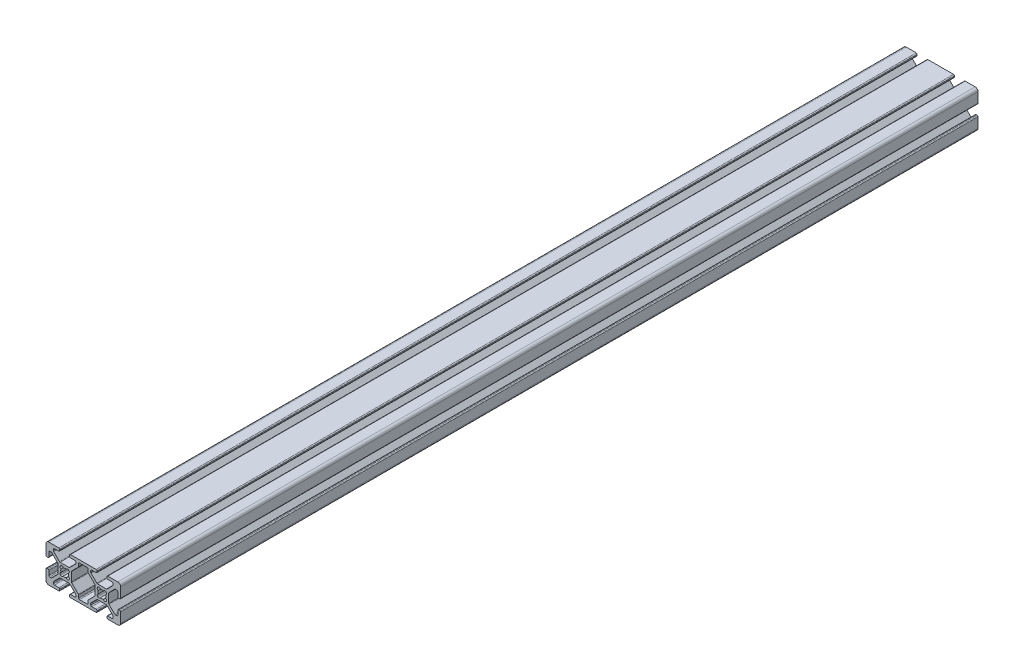
SolidWorks part; units mm, degrees
material "6105-T5 Aluminum"
ref_plane "Front Plane" through (0, 0, 0) normal (0, 0, 1) x (1, 0, 0)
ref_plane "Top Plane" through (0, 0, 0) normal (0, 1, 0) x (1, 0, 0)
ref_plane "Right Plane" through (0, 0, 0) normal (1, 0, 0) x (0, 0, -1)
sketch "Sketch1" plane through (0, 0, 0) normal (0, 0, 1) x (1, 0, 0)
  line L0 (-2.1249, -2.3045) -> (-2.3045, -2.1249)
  line L1 (-2.3045, 2.1249) -> (-2.1249, 2.3045)
  line L2 (2.1249, 2.3045) -> (2.3045, 2.1249)
  line L3 (2.3045, -2.1249) -> (2.1249, -2.3045)
  line L4 (-12.505, -7.992) -> (-12.505, -6.6448)
  line L5 (-12.6538, -6.2856) -> (-16.1962, -2.7431)
  line L6 (-16.345, -2.3839) -> (-16.345, 2.3839)
  line L7 (-16.1962, 2.7431) -> (-12.6538, 6.2856)
  line L8 (-12.505, 6.6448) -> (-12.505, 7.992)
  line L9 (-11.997, 8.5) -> (-8.003, 8.5)
  line L10 (-7.495, 7.992) -> (-7.495, 6.6448)
  line L11 (-7.3462, 6.2856) -> (-3.8038, 2.7431)
  line L12 (-3.655, 2.3839) -> (-3.655, -2.3839)
  line L13 (-3.8038, -2.7431) -> (-7.3462, -6.2856)
  line L14 (-7.495, -6.6448) -> (-7.495, -7.992)
  line L15 (-8.003, -8.5) -> (-11.997, -8.5)
  line L16 (-22.1249, -2.3045) -> (-22.3045, -2.1249)
  line L17 (-22.3045, 2.1249) -> (-22.1249, 2.3045)
  line L18 (-17.8751, 2.3045) -> (-17.6955, 2.1249)
  line L19 (-17.6955, -2.1249) -> (-17.8751, -2.3045)
  line L20 (-22.3839, -3.655) -> (-17.6161, -3.655)
  line L21 (-17.2569, -3.8038) -> (-14.1538, -6.9069)
  line L22 (-14.005, -7.2661) -> (-14.005, -7.992)
  line L23 (-14.513, -8.5) -> (-16.862, -8.5)
  line L24 (-17.37, -9.008) -> (-17.37, -9.492)
  line L25 (-16.862, -10) -> (-3.138, -10)
  line L26 (-2.63, -9.492) -> (-2.63, -9.008)
  line L27 (-3.138, -8.5) -> (-5.487, -8.5)
  line L28 (-5.995, -7.992) -> (-5.995, -7.2661)
  line L29 (-5.8462, -6.9069) -> (-2.7431, -3.8038)
  line L30 (-2.3839, -3.655) -> (2.3839, -3.655)
  line L31 (2.7431, -3.8038) -> (5.8462, -6.9069)
  line L32 (5.995, -7.2661) -> (5.995, -7.992)
  line L33 (5.487, -8.5) -> (3.138, -8.5)
  line L34 (2.63, -9.008) -> (2.63, -9.492)
  line L35 (3.138, -10) -> (8.5, -10)
  line L36 (10, -8.5) -> (10, -3.138)
  line L37 (9.492, -2.63) -> (9.008, -2.63)
  line L38 (8.5, -3.138) -> (8.5, -5.487)
  line L39 (7.992, -5.995) -> (7.2661, -5.995)
  line L40 (6.9069, -5.8462) -> (3.8038, -2.7431)
  line L41 (3.655, -2.3839) -> (3.655, 2.3839)
  line L42 (3.8038, 2.7431) -> (6.9069, 5.8462)
  line L43 (7.2661, 5.995) -> (7.992, 5.995)
  line L44 (8.5, 5.487) -> (8.5, 3.138)
  line L45 (9.008, 2.63) -> (9.492, 2.63)
  line L46 (10, 3.138) -> (10, 8.5)
  line L47 (8.5, 10) -> (3.138, 10)
  line L48 (2.63, 9.492) -> (2.63, 9.008)
  line L49 (3.138, 8.5) -> (5.487, 8.5)
  line L50 (5.995, 7.992) -> (5.995, 7.2661)
  line L51 (5.8462, 6.9069) -> (2.7431, 3.8038)
  line L52 (2.3839, 3.655) -> (-2.3839, 3.655)
  line L53 (-2.7431, 3.8038) -> (-5.8462, 6.9069)
  line L54 (-5.995, 7.2661) -> (-5.995, 7.992)
  line L55 (-5.487, 8.5) -> (-3.138, 8.5)
  line L56 (-2.63, 9.008) -> (-2.63, 9.492)
  line L57 (-3.138, 10) -> (-16.862, 10)
  line L58 (-17.37, 9.492) -> (-17.37, 9.008)
  line L59 (-16.862, 8.5) -> (-14.513, 8.5)
  line L60 (-14.005, 7.992) -> (-14.005, 7.2661)
  line L61 (-14.1538, 6.9069) -> (-17.2569, 3.8038)
  line L62 (-17.6161, 3.655) -> (-22.3839, 3.655)
  line L63 (-22.7431, 3.8038) -> (-25.8462, 6.9069)
  line L64 (-25.995, 7.2661) -> (-25.995, 7.992)
  line L65 (-25.487, 8.5) -> (-23.138, 8.5)
  line L66 (-22.63, 9.008) -> (-22.63, 9.492)
  line L67 (-23.138, 10) -> (-28.5, 10)
  line L68 (-30, 8.5) -> (-30, 3.138)
  line L69 (-29.492, 2.63) -> (-29.008, 2.63)
  line L70 (-28.5, 3.138) -> (-28.5, 5.487)
  line L71 (-27.992, 5.995) -> (-27.2661, 5.995)
  line L72 (-26.9069, 5.8462) -> (-23.8038, 2.7431)
  line L73 (-23.655, 2.3839) -> (-23.655, -2.3839)
  line L74 (-23.8038, -2.7431) -> (-26.9069, -5.8462)
  line L75 (-27.2661, -5.995) -> (-27.992, -5.995)
  line L76 (-28.5, -5.487) -> (-28.5, -3.138)
  line L77 (-29.008, -2.63) -> (-29.492, -2.63)
  line L78 (-30, -3.138) -> (-30, -8.5)
  line L79 (-28.5, -10) -> (-23.138, -10)
  line L80 (-22.63, -9.492) -> (-22.63, -9.008)
  line L81 (-23.138, -8.5) -> (-25.487, -8.5)
  line L82 (-25.995, -7.992) -> (-25.995, -7.2661)
  line L83 (-25.8462, -6.9069) -> (-22.7431, -3.8038)
  arc A0 (-1.9351, -0.804) -> (-2.3045, -2.1249) centre (-1.748, -1.5684) ccw
  arc A1 (-1.9351, 0.804) -> (-1.9351, -0.804) centre (0, 0) ccw
  arc A2 (-2.3045, 2.1249) -> (-1.9351, 0.804) centre (-1.748, 1.5684) ccw
  arc A3 (-0.804, 1.9351) -> (-2.1249, 2.3045) centre (-1.5684, 1.748) ccw
  arc A4 (0.804, 1.9351) -> (-0.804, 1.9351) centre (0, 0) ccw
  arc A5 (2.1249, 2.3045) -> (0.804, 1.9351) centre (1.5684, 1.748) ccw
  arc A6 (1.9351, 0.804) -> (2.3045, 2.1249) centre (1.748, 1.5684) ccw
  arc A7 (1.9351, -0.804) -> (1.9351, 0.804) centre (0, 0) ccw
  arc A8 (2.3045, -2.1249) -> (1.9351, -0.804) centre (1.748, -1.5684) ccw
  arc A9 (0.804, -1.9351) -> (2.1249, -2.3045) centre (1.5684, -1.748) ccw
  arc A10 (-0.804, -1.9351) -> (0.804, -1.9351) centre (0, 0) ccw
  arc A11 (-2.1249, -2.3045) -> (-0.804, -1.9351) centre (-1.5684, -1.748) ccw
  arc A12 (-12.505, -7.992) -> (-11.997, -8.5) centre (-11.997, -7.992) ccw
  arc A13 (-12.505, -6.6448) -> (-12.6538, -6.2856) centre (-13.013, -6.6448) ccw
  arc A14 (-16.345, -2.3839) -> (-16.1962, -2.7431) centre (-15.837, -2.3839) ccw
  arc A15 (-16.1962, 2.7431) -> (-16.345, 2.3839) centre (-15.837, 2.3839) ccw
  arc A16 (-12.6538, 6.2856) -> (-12.505, 6.6448) centre (-13.013, 6.6448) ccw
  arc A17 (-11.997, 8.5) -> (-12.505, 7.992) centre (-11.997, 7.992) ccw
  arc A18 (-7.495, 7.992) -> (-8.003, 8.5) centre (-8.003, 7.992) ccw
  arc A19 (-7.495, 6.6448) -> (-7.3462, 6.2856) centre (-6.987, 6.6448) ccw
  arc A20 (-3.655, 2.3839) -> (-3.8038, 2.7431) centre (-4.163, 2.3839) ccw
  arc A21 (-3.8038, -2.7431) -> (-3.655, -2.3839) centre (-4.163, -2.3839) ccw
  arc A22 (-7.3462, -6.2856) -> (-7.495, -6.6448) centre (-6.987, -6.6448) ccw
  arc A23 (-8.003, -8.5) -> (-7.495, -7.992) centre (-8.003, -7.992) ccw
  arc A24 (-21.9351, -0.804) -> (-22.3045, -2.1249) centre (-21.748, -1.5684) ccw
  arc A25 (-21.9351, 0.804) -> (-21.9351, -0.804) centre (-20, 0) ccw
  arc A26 (-22.3045, 2.1249) -> (-21.9351, 0.804) centre (-21.748, 1.5684) ccw
  arc A27 (-20.804, 1.9351) -> (-22.1249, 2.3045) centre (-21.5684, 1.748) ccw
  arc A28 (-19.196, 1.9351) -> (-20.804, 1.9351) centre (-20, 0) ccw
  arc A29 (-17.8751, 2.3045) -> (-19.196, 1.9351) centre (-18.4316, 1.748) ccw
  arc A30 (-18.0649, 0.804) -> (-17.6955, 2.1249) centre (-18.252, 1.5684) ccw
  arc A31 (-18.0649, -0.804) -> (-18.0649, 0.804) centre (-20, 0) ccw
  arc A32 (-17.6955, -2.1249) -> (-18.0649, -0.804) centre (-18.252, -1.5684) ccw
  arc A33 (-19.196, -1.9351) -> (-17.8751, -2.3045) centre (-18.4316, -1.748) ccw
  arc A34 (-20.804, -1.9351) -> (-19.196, -1.9351) centre (-20, 0) ccw
  arc A35 (-22.1249, -2.3045) -> (-20.804, -1.9351) centre (-21.5684, -1.748) ccw
  arc A36 (-22.3839, -3.655) -> (-22.7431, -3.8038) centre (-22.3839, -4.163) ccw
  arc A37 (-17.2569, -3.8038) -> (-17.6161, -3.655) centre (-17.6161, -4.163) ccw
  arc A38 (-14.005, -7.2661) -> (-14.1538, -6.9069) centre (-14.513, -7.2661) ccw
  arc A39 (-14.513, -8.5) -> (-14.005, -7.992) centre (-14.513, -7.992) ccw
  arc A40 (-16.862, -8.5) -> (-17.37, -9.008) centre (-16.862, -9.008) ccw
  arc A41 (-17.37, -9.492) -> (-16.862, -10) centre (-16.862, -9.492) ccw
  arc A42 (-3.138, -10) -> (-2.63, -9.492) centre (-3.138, -9.492) ccw
  arc A43 (-2.63, -9.008) -> (-3.138, -8.5) centre (-3.138, -9.008) ccw
  arc A44 (-5.995, -7.992) -> (-5.487, -8.5) centre (-5.487, -7.992) ccw
  arc A45 (-5.8462, -6.9069) -> (-5.995, -7.2661) centre (-5.487, -7.2661) ccw
  arc A46 (-2.3839, -3.655) -> (-2.7431, -3.8038) centre (-2.3839, -4.163) ccw
  arc A47 (2.7431, -3.8038) -> (2.3839, -3.655) centre (2.3839, -4.163) ccw
  arc A48 (5.995, -7.2661) -> (5.8462, -6.9069) centre (5.487, -7.2661) ccw
  arc A49 (5.487, -8.5) -> (5.995, -7.992) centre (5.487, -7.992) ccw
  arc A50 (3.138, -8.5) -> (2.63, -9.008) centre (3.138, -9.008) ccw
  arc A51 (2.63, -9.492) -> (3.138, -10) centre (3.138, -9.492) ccw
  arc A52 (8.5, -10) -> (10, -8.5) centre (8.5, -8.5) ccw
  arc A53 (10, -3.138) -> (9.492, -2.63) centre (9.492, -3.138) ccw
  arc A54 (9.008, -2.63) -> (8.5, -3.138) centre (9.008, -3.138) ccw
  arc A55 (7.992, -5.995) -> (8.5, -5.487) centre (7.992, -5.487) ccw
  arc A56 (6.9069, -5.8462) -> (7.2661, -5.995) centre (7.2661, -5.487) ccw
  arc A57 (3.655, -2.3839) -> (3.8038, -2.7431) centre (4.163, -2.3839) ccw
  arc A58 (3.8038, 2.7431) -> (3.655, 2.3839) centre (4.163, 2.3839) ccw
  arc A59 (7.2661, 5.995) -> (6.9069, 5.8462) centre (7.2661, 5.487) ccw
  arc A60 (8.5, 5.487) -> (7.992, 5.995) centre (7.992, 5.487) ccw
  arc A61 (8.5, 3.138) -> (9.008, 2.63) centre (9.008, 3.138) ccw
  arc A62 (9.492, 2.63) -> (10, 3.138) centre (9.492, 3.138) ccw
  arc A63 (10, 8.5) -> (8.5, 10) centre (8.5, 8.5) ccw
  arc A64 (3.138, 10) -> (2.63, 9.492) centre (3.138, 9.492) ccw
  arc A65 (2.63, 9.008) -> (3.138, 8.5) centre (3.138, 9.008) ccw
  arc A66 (5.995, 7.992) -> (5.487, 8.5) centre (5.487, 7.992) ccw
  arc A67 (5.8462, 6.9069) -> (5.995, 7.2661) centre (5.487, 7.2661) ccw
  arc A68 (2.3839, 3.655) -> (2.7431, 3.8038) centre (2.3839, 4.163) ccw
  arc A69 (-2.7431, 3.8038) -> (-2.3839, 3.655) centre (-2.3839, 4.163) ccw
  arc A70 (-5.995, 7.2661) -> (-5.8462, 6.9069) centre (-5.487, 7.2661) ccw
  arc A71 (-5.487, 8.5) -> (-5.995, 7.992) centre (-5.487, 7.992) ccw
  arc A72 (-3.138, 8.5) -> (-2.63, 9.008) centre (-3.138, 9.008) ccw
  arc A73 (-2.63, 9.492) -> (-3.138, 10) centre (-3.138, 9.492) ccw
  arc A74 (-16.862, 10) -> (-17.37, 9.492) centre (-16.862, 9.492) ccw
  arc A75 (-17.37, 9.008) -> (-16.862, 8.5) centre (-16.862, 9.008) ccw
  arc A76 (-14.005, 7.992) -> (-14.513, 8.5) centre (-14.513, 7.992) ccw
  arc A77 (-14.1538, 6.9069) -> (-14.005, 7.2661) centre (-14.513, 7.2661) ccw
  arc A78 (-17.6161, 3.655) -> (-17.2569, 3.8038) centre (-17.6161, 4.163) ccw
  arc A79 (-22.7431, 3.8038) -> (-22.3839, 3.655) centre (-22.3839, 4.163) ccw
  arc A80 (-25.995, 7.2661) -> (-25.8462, 6.9069) centre (-25.487, 7.2661) ccw
  arc A81 (-25.487, 8.5) -> (-25.995, 7.992) centre (-25.487, 7.992) ccw
  arc A82 (-23.138, 8.5) -> (-22.63, 9.008) centre (-23.138, 9.008) ccw
  arc A83 (-22.63, 9.492) -> (-23.138, 10) centre (-23.138, 9.492) ccw
  arc A84 (-28.5, 10) -> (-30, 8.5) centre (-28.5, 8.5) ccw
  arc A85 (-30, 3.138) -> (-29.492, 2.63) centre (-29.492, 3.138) ccw
  arc A86 (-29.008, 2.63) -> (-28.5, 3.138) centre (-29.008, 3.138) ccw
  arc A87 (-27.992, 5.995) -> (-28.5, 5.487) centre (-27.992, 5.487) ccw
  arc A88 (-26.9069, 5.8462) -> (-27.2661, 5.995) centre (-27.2661, 5.487) ccw
  arc A89 (-23.655, 2.3839) -> (-23.8038, 2.7431) centre (-24.163, 2.3839) ccw
  arc A90 (-23.8038, -2.7431) -> (-23.655, -2.3839) centre (-24.163, -2.3839) ccw
  arc A91 (-27.2661, -5.995) -> (-26.9069, -5.8462) centre (-27.2661, -5.487) ccw
  arc A92 (-28.5, -5.487) -> (-27.992, -5.995) centre (-27.992, -5.487) ccw
  arc A93 (-28.5, -3.138) -> (-29.008, -2.63) centre (-29.008, -3.138) ccw
  arc A94 (-29.492, -2.63) -> (-30, -3.138) centre (-29.492, -3.138) ccw
  arc A95 (-30, -8.5) -> (-28.5, -10) centre (-28.5, -8.5) ccw
  arc A96 (-23.138, -10) -> (-22.63, -9.492) centre (-23.138, -9.492) ccw
  arc A97 (-22.63, -9.008) -> (-23.138, -8.5) centre (-23.138, -9.008) ccw
  arc A98 (-25.995, -7.992) -> (-25.487, -8.5) centre (-25.487, -7.992) ccw
  arc A99 (-25.8462, -6.9069) -> (-25.995, -7.2661) centre (-25.487, -7.2661) ccw
extrude "Extrude1" add sketch "Sketch1" against normal blind 460
